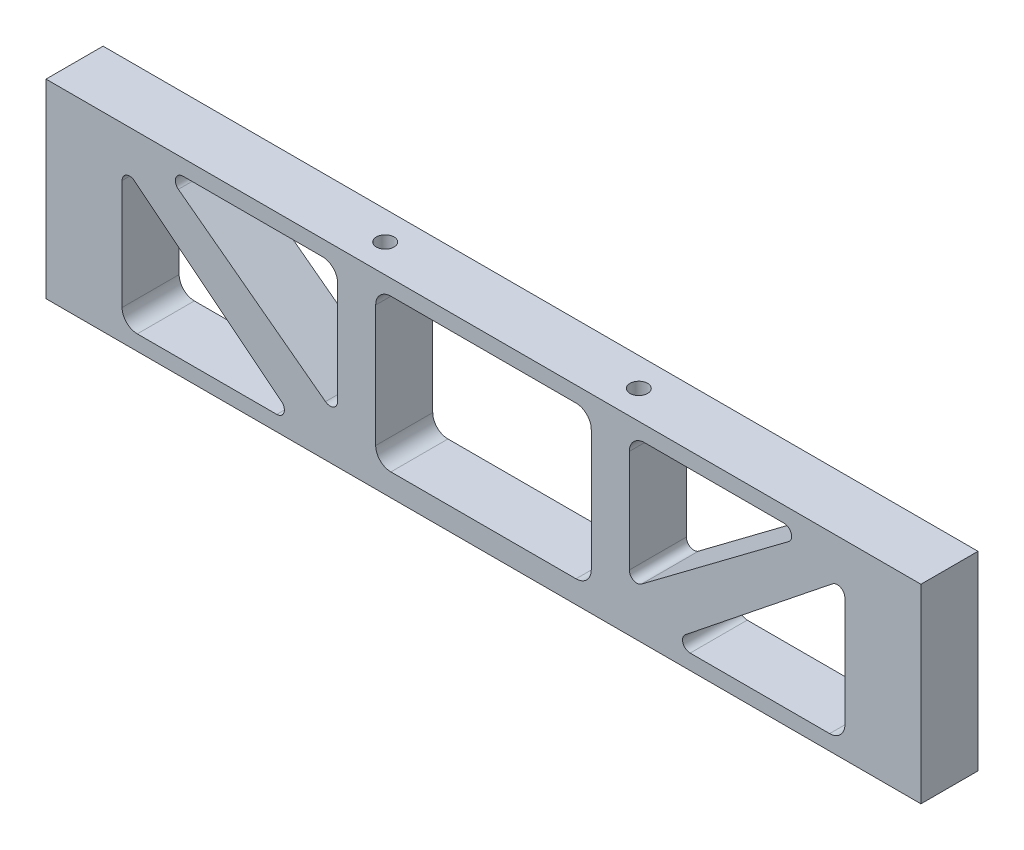
SolidWorks part; units mm, degrees
material "PE High Density"
ref_plane "Front Plane" through (0, 0, 0) normal (0, 0, 1) x (1, 0, 0)
ref_plane "Top Plane" through (0, 0, 0) normal (0, 1, 0) x (1, 0, 0)
ref_plane "Right Plane" through (0, 0, 0) normal (1, 0, 0) x (0, 0, -1)
sketch "Sketch1" plane through (0, 0, 0) normal (0, 0, 1) x (1, 0, 0)
  line L0 (-24.3417, 15.875) -> (-24.3417, -15.875) construction
  line L1 (-73.025, 15.875) -> (73.025, 15.875)
  line L2 (-73.025, 15.875) -> (-73.025, -15.875)
  line L3 (-73.025, -15.875) -> (73.025, -15.875)
  line L4 (73.025, 15.875) -> (73.025, -15.875)
  line L5 (-73.025, 15.875) -> (73.025, -15.875) construction
  line L6 (-73.025, -15.875) -> (73.025, 15.875) construction
  line L7 (24.3417, 15.875) -> (24.3417, -15.875) construction
  line L9 (-69.85, -12.7) -> (-27.5167, 12.7) construction
  line L10 (-69.85, -12.7) -> (-69.85, 12.7) construction
  line L11 (-64.3071, -11.2256) -> (-29.9209, 9.4061)
  line L12 (-73.025, -15.875) -> (-24.3417, -15.875)
  line L13 (-73.025, -15.875) -> (-73.025, 15.875)
  line L14 (-73.025, 15.875) -> (-24.3417, 15.875)
  line L15 (-24.3417, -15.875) -> (-24.3417, 15.875) construction
  line L16 (-69.85, 12.7) -> (-27.5167, 12.7) construction
  line L17 (-27.5167, -12.7) -> (-27.5167, 12.7) construction
  line L18 (-69.85, -12.7) -> (-27.5167, -12.7) construction
  line L19 (-67.4457, -9.4061) -> (-33.0595, 11.2256)
  line L20 (-69.0332, -14.0613) -> (-26.6999, 11.3387) construction
  line L21 (-69.85, -8.0448) -> (-69.85, 11.1125)
  line L22 (-70.6668, -11.3387) -> (-28.3334, 14.0613) construction
  line L23 (-68.2625, 12.7) -> (-33.4679, 12.7)
  line L24 (-63.8988, -12.7) -> (-29.1042, -12.7)
  line L25 (-27.5167, -11.1125) -> (-27.5167, 8.0448)
  line L26 (-15.6238, -11.2256) -> (18.7624, 9.4061)
  line L27 (-18.7624, -9.4061) -> (15.6238, 11.2256)
  line L28 (-21.1667, -8.0448) -> (-21.1667, 11.1125)
  line L29 (-19.5792, 12.7) -> (15.2154, 12.7)
  line L30 (-15.2154, -12.7) -> (19.5792, -12.7)
  line L31 (21.1667, -11.1125) -> (21.1667, 8.0448)
  line L32 (-21.1667, -12.7) -> (21.1667, 12.7) construction
  line L33 (-21.1667, -12.7) -> (-21.1667, 12.7) construction
  line L34 (-21.1667, 12.7) -> (21.1667, 12.7) construction
  line L35 (21.1667, -12.7) -> (21.1667, 12.7) construction
  line L36 (-21.1667, -12.7) -> (21.1667, -12.7) construction
  line L37 (33.0595, -11.2256) -> (67.4457, 9.4061)
  line L38 (29.9209, -9.4061) -> (64.3071, 11.2256)
  line L39 (27.5167, -8.0448) -> (27.5167, 11.1125)
  line L40 (29.1042, 12.7) -> (63.8988, 12.7)
  line L41 (33.4679, -12.7) -> (68.2625, -12.7)
  line L42 (69.85, -11.1125) -> (69.85, 8.0448)
  line L43 (27.5167, -12.7) -> (69.85, 12.7) construction
  line L44 (27.5167, -12.7) -> (27.5167, 12.7) construction
  line L45 (27.5167, 12.7) -> (69.85, 12.7) construction
  line L46 (69.85, -12.7) -> (69.85, 12.7) construction
  line L47 (27.5167, -12.7) -> (69.85, -12.7) construction
  line L59 (-64.3071, -11.2256) -> (-15.6238, -11.2256) construction
  line L60 (-69.85, 15.875) -> (-69.85, -15.875)
  arc A0 (-33.4679, 12.7) -> (-33.0595, 11.2256) centre (-33.4679, 11.9062) cw
  arc A1 (-69.85, -8.0448) -> (-67.4457, -9.4061) centre (-68.2625, -8.0448) ccw
  arc A2 (-69.85, 11.1125) -> (-68.2625, 12.7) centre (-68.2625, 11.1125) cw
  arc A3 (-27.5167, 8.0448) -> (-29.9209, 9.4061) centre (-29.1042, 8.0448) ccw
  arc A4 (-63.8988, -12.7) -> (-64.3071, -11.2256) centre (-63.8988, -11.9062) cw
  arc A5 (-27.5167, -11.1125) -> (-29.1042, -12.7) centre (-29.1042, -11.1125) cw
  arc A6 (15.2154, 12.7) -> (15.6238, 11.2256) centre (15.2154, 11.9062) cw
  arc A7 (-21.1667, -8.0448) -> (-18.7624, -9.4061) centre (-19.5792, -8.0448) ccw
  arc A8 (-21.1667, 11.1125) -> (-19.5792, 12.7) centre (-19.5792, 11.1125) cw
  arc A9 (21.1667, 8.0448) -> (18.7624, 9.4061) centre (19.5792, 8.0448) ccw
  arc A10 (-15.2154, -12.7) -> (-15.6238, -11.2256) centre (-15.2154, -11.9062) cw
  arc A11 (21.1667, -11.1125) -> (19.5792, -12.7) centre (19.5792, -11.1125) cw
  arc A12 (63.8988, 12.7) -> (64.3071, 11.2256) centre (63.8988, 11.9062) cw
  arc A13 (27.5167, -8.0448) -> (29.9209, -9.4061) centre (29.1042, -8.0448) ccw
  arc A14 (27.5167, 11.1125) -> (29.1042, 12.7) centre (29.1042, 11.1125) cw
  arc A15 (69.85, 8.0448) -> (67.4457, 9.4061) centre (68.2625, 8.0448) ccw
  arc A16 (33.4679, -12.7) -> (33.0595, -11.2256) centre (33.4679, -11.9062) cw
  arc A17 (69.85, -11.1125) -> (68.2625, -12.7) centre (68.2625, -11.1125) cw
  point P0 (0, 0)
  point P26 (-30.6022, 12.7)
  point P29 (-69.85, -10.8487)
  point P35 (-27.5167, 10.8487)
  point P38 (-66.7645, -12.7)
  dimension "D7" = 0.7937
  dimension "D8" = 1.5875
  dimension "D9" = 1.5875
  dimension "D10" = 1.5875
  dimension "D11" = 0.7937
  dimension "D12" = 1.5875
  dimension "D1" = 31.75
  dimension "CrossBraceLength" = 146.05
  dimension "D4" = 48.6833
  dimension "D14" = 48.6833
  dimension "D6" = 3.175
  dimension "D2" = 1.5875
  dimension "D5" = 1.5875
  dimension "D3" = 3
  dimension "D13" = 3
extrude "Boss-Extrude1" [suppressed] add sketch "Sketch1" along normal blind 9.525
sketch "Sketch2" plane through (0, 0, 0) normal (0, 0, 1) x (1, 0, 0)
  line L0 (-63.5, 15.3) -> (-63.5, -16.45) construction
  line L1 (-73.025, 15.3) -> (73.025, 15.3)
  line L2 (-73.025, 15.3) -> (-73.025, -16.45)
  line L3 (-73.025, -16.45) -> (73.025, -16.45)
  line L4 (73.025, 15.3) -> (73.025, -16.45)
  line L5 (-73.025, 15.3) -> (73.025, -16.45) construction
  line L6 (-73.025, -16.45) -> (73.025, 15.3) construction
  line L7 (0, 15.3) -> (0, -16.45) construction
  line L8 (-63.5, -16.45) -> (-63.5, 15.3) construction
  line L9 (63.5, 15.3) -> (63.5, -16.45) construction
  line L10 (-21.1667, 15.3) -> (-21.1667, -16.45) construction
  line L11 (-73.025, -0.575) -> (73.025, -0.575) construction
  line L12 (21.1667, 15.3) -> (21.1667, -16.45) construction
  line L14 (-63.5, -16.45) -> (-63.5, 15.3) construction
  line L15 (-63.5, 15.3) -> (-21.1667, 15.3)
  line L19 (-63.5, 15.3) -> (-21.1667, -16.45) construction
  line L20 (-63.5, -16.45) -> (-21.1667, -16.45)
  line L21 (-21.1667, 15.3) -> (-63.5, 15.3)
  line L22 (-63.5, -16.45) -> (-21.1667, -16.45)
  line L23 (-63.5, -16.45) -> (-63.5, 15.3) construction
  line L27 (-63.5, 15.3) -> (-21.1667, -16.45) construction
  line L28 (-50.927, 10.414) -> (-26.3737, -8.001)
  line L29 (-60.325, -11.3725) -> (-60.325, 6.985)
  line L48 (-57.785, -13.9125) -> (-34.5017, -13.9125)
  line L67 (-68.2625, 15.3) -> (-68.2625, -16.45) construction
  line L78 (-58.262, 7.977) -> (-33.7087, -11.6505)
  line L85 (68.2625, 15.875) -> (68.2625, -15.875) construction
  line L96 (73.025, 15.3) -> (73.025, -16.45)
  line L97 (-63.5, 15.3) -> (-24.3417, 15.3)
  line L99 (-60.325, -16.45) -> (-60.325, 15.3) construction
  line L102 (-24.3417, 10.16) -> (-24.3417, -6.985)
  line L104 (-50.165, 12.7) -> (-26.8817, 12.7)
  line L105 (24.3417, 10.16) -> (24.3417, -6.985)
  line L106 (-24.3417, 15.3) -> (-24.3417, -16.45) construction
  line L107 (50.165, 12.7) -> (26.8817, 12.7)
  line L108 (50.927, 10.414) -> (26.3737, -8.001)
  line L109 (57.785, -13.9125) -> (34.5017, -13.9125)
  line L110 (58.262, 7.977) -> (33.7087, -11.6505)
  line L111 (60.325, -11.3725) -> (60.325, 6.985)
  line L112 (0, -16.45) -> (0, -13.275)
  line L114 (-15.4517, 12.7) -> (15.4517, 12.7)
  line L115 (-17.9917, 10.16) -> (-17.9917, -10.16)
  line L116 (-15.4517, -12.7) -> (15.4517, -12.7)
  line L117 (17.9917, 10.16) -> (17.9917, -10.16)
  line L118 (-17.9917, 12.7) -> (17.9917, -12.7) construction
  line L119 (-17.9917, -12.7) -> (17.9917, 12.7) construction
  arc A52 (-57.785, -13.9125) -> (-60.325, -11.3725) centre (-57.785, -11.3725) cw
  arc A53 (-60.325, 6.985) -> (-58.262, 7.977) centre (-59.055, 6.985) cw
  arc A54 (-34.5017, -13.9125) -> (-33.7087, -11.6505) centre (-34.5017, -12.6425) ccw
  arc A55 (-26.8817, 12.7) -> (-24.3417, 10.16) centre (-26.8817, 10.16) cw
  arc A56 (-26.3737, -8.001) -> (-24.3417, -6.985) centre (-25.6117, -6.985) ccw
  arc A57 (-50.927, 10.414) -> (-50.165, 12.7) centre (-50.165, 11.43) cw
  arc A58 (26.3737, -8.001) -> (24.3417, -6.985) centre (25.6117, -6.985) cw
  arc A59 (26.8817, 12.7) -> (24.3417, 10.16) centre (26.8817, 10.16) ccw
  arc A60 (50.927, 10.414) -> (50.165, 12.7) centre (50.165, 11.43) ccw
  arc A61 (57.785, -13.9125) -> (60.325, -11.3725) centre (57.785, -11.3725) ccw
  arc A62 (34.5017, -13.9125) -> (33.7087, -11.6505) centre (34.5017, -12.6425) cw
  arc A63 (60.325, 6.985) -> (58.262, 7.977) centre (59.055, 6.985) ccw
  arc A64 (-15.4517, -12.7) -> (-17.9917, -10.16) centre (-15.4517, -10.16) cw
  arc A65 (-17.9917, 10.16) -> (-15.4517, 12.7) centre (-15.4517, 10.16) cw
  arc A66 (17.9917, 10.16) -> (15.4517, 12.7) centre (15.4517, 10.16) ccw
  arc A67 (17.9917, -10.16) -> (15.4517, -12.7) centre (15.4517, -10.16) cw
  point P18 (-65.405, 13.335)
  point P19 (-23.0717, -18.415)
  point P24 (-63.5, 12.7)
  point P26 (-24.3417, 12.7)
  point P34 (-61.595, 18.415)
  point P36 (-19.2617, -13.335)
  point P65 (0, 0)
  dimension "D6" = 2.54
  dimension "D8" = 1.27
  dimension "D9" = 1.27
  dimension "D11" = 2.54
  dimension "D12" = 1.27
  dimension "D13" = 1.27
  dimension "D16" = 2.54
  dimension "D1" = 146.05
  dimension "D2" = 31.75
  dimension "D3" = 9.525
  dimension "D23" = 4.7625
  dimension "D4" = 42.3333
  dimension "D5" = 42.3333
  dimension "D14" = 3.175
  dimension "D15" = 35.9833
  dimension "D7" = 3.175
  dimension "D10" = 3.175
extrude "Boss-Extrude2" add sketch "Sketch2" along normal blind 9.525
sketch "Sketch3" plane through (-73.025, 0, 0) normal (-1, 0, 0) x (0, 0, 1)
  line L0 (9.525, 15.3) -> (0, 15.3) construction
  line L1 (0, -0.575) -> (9.525, -0.575) construction
  line L3 (4.7625, -16.45) -> (4.7625, 15.3) construction
  line L4 (9.525, -16.45) -> (0, -16.45) construction
  line L5 (0, 15.3) -> (0, -16.45) construction
  line L6 (9.525, 15.3) -> (9.525, -16.45) construction
  circle A0 centre (4.7625, 8) radius 2.2479
  circle A1 centre (4.7625, -9.15) radius 2.2479
  dimension "D2" = 4.4958
  dimension "D1" = 7.3
extrude "Cut-Extrude1" [suppressed] cut sketch "Sketch3" against normal blind 11.1125
sketch "Sketch4" plane through (0, 15.3, 0) normal (0, 1, 0) x (1, 0, 0)
  line L2 (17.9917, -9.525) -> (17.9917, 0) construction
  line L3 (17.9917, -9.525) -> (17.9917, 0) construction
  line L4 (73.025, 0) -> (-73.025, 0)
  line L5 (-73.025, 0) -> (-73.025, -9.525)
  line L6 (-73.025, -9.525) -> (73.025, -9.525)
  line L7 (73.025, -9.525) -> (73.025, 0)
  line L8 (73.025, 0) -> (-73.025, 0) construction
  line L9 (-73.025, 0) -> (-73.025, -9.525) construction
  line L10 (-73.025, -9.525) -> (73.025, -9.525) construction
  line L11 (73.025, -9.525) -> (73.025, 0) construction
  line L12 (-17.9917, -9.525) -> (-17.9917, 0) construction
  line L13 (-17.9917, -9.525) -> (-17.9917, 0) construction
  line L14 (-24.3417, -9.525) -> (-24.3417, 0) construction
  line L15 (-24.3417, -9.525) -> (-24.3417, 0) construction
  line L16 (24.3417, -9.525) -> (24.3417, 0) construction
  line L17 (24.3417, -9.525) -> (24.3417, 0) construction
  line L18 (24.3417, -9.525) -> (17.9917, 0) construction
  line L19 (17.9917, -9.525) -> (24.3417, 0) construction
  circle A0 centre (21.1667, -4.7625) radius 1.4732
  dimension "D2" = 2.9464
  dimension "D1" = 0
extrude "Cut-Extrude2" cut sketch "Sketch4" against normal blind 12.7 contours A0
ref_plane "Plane1" through (0, -0.575, 0) normal (0, 1, 0) x (1, 0, 0)
mirror "Mirror2" about plane through (0, -0.575, 0) normal (0, 1, 0) of "Cut-Extrude2" second plane through (0, 0, 0) second plane normal (1, 0, 0)
mirror "Mirror3" [suppressed] about plane through (0, 0, 0) normal (1, 0, 0)
equation "\"Plate Width\" = 3.5in"
equation "\"Plate Thickness\" = 0.375in"
equation "\"Num holes\" = 4"
equation "\"Plate Height\" = 1.25in"
equation "\"Top Plate Width\" = 4.5in"
equation "\"Plate Clearance Hole Diameter\" = 0.125in"
equation "\"Plate Tap Hole Diameter\" = 0.116in"
equation "\"Bottom Plate Length\" = 6.5in"
equation "\"CrossBraceLength@Sketch1\" = \"Bottom Plate Length\" - 2 * \"Plate Thickness\""
equation "\"D1@Sketch1\"=\"Plate Height\""
equation "\"num_triangle_holes\"= 3"
equation "\"D3@Sketch1\"=\"num_triangle_holes\""
equation "\"D4@Sketch1\"=( \"Bottom Plate Length\" - 2 * \"Plate Thickness\" ) / \"num_triangle_holes\""
equation "\"BorderThickness\"= 0.125"
equation "\"D6@Sketch1\"=\"BorderThickness\""
equation "\"D2@Sketch1\"=\"BorderThickness\"/2"
equation "\"D9@Sketch1\"=\"BorderThickness\"/2"
equation "\"D8@Sketch1\"=\"BorderThickness\"/2"
equation "\"D7@Sketch1\"=\"BorderThickness\"/4"
equation "\"D10@Sketch1\"=\"BorderThickness\"/2"
equation "\"D11@Sketch1\"=\"BorderThickness\"/4"
equation "\"D12@Sketch1\"=\"BorderThickness\"/2"
equation "\"D13@Sketch1\"=\"num_triangle_holes\""
equation "\"D14@Sketch1\"=( \"Bottom Plate Length\" - 2 * \"Plate Thickness\" ) / \"num_triangle_holes\""
equation "\"D1@Boss-Extrude1\"=\"Plate Thickness\""
equation "\"D1@Sketch2\"=\"Bottom Plate Length\" - 2 * \"Plate Thickness\""
equation "\"D2@Sketch2\"=\"Plate Height\""
equation "\"wall_thickness\"= 0.375"
equation "\"D3@Sketch2\"=\"wall_thickness\""
equation "\"D1@Boss-Extrude2\"=\"Plate Thickness\""
equation "\"D23@Sketch2\"=\"wall_thickness\"/2"
equation "\"Number Eight Clearance Size\" = 0.177in"
equation "\"D2@Sketch3\"=\"Number Eight Clearance Size\""
equation "\"D1@Cut-Extrude1\"=(0.75 - \"Plate Thickness\") + 0.0625"
equation "\"D4@Sketch2\"=( ( \"Bottom Plate Length\" - 2 * \"Plate Thickness\" ) - \"Plate Thickness\" * 2 ) /3"
equation "\"D5@Sketch2\"=( ( \"Bottom Plate Length\" - 2 * \"Plate Thickness\" ) - \"Plate Thickness\" * 2 ) /3"
equation "\"D14@Sketch2\"=\"BorderThickness\""
equation "\"D15@Sketch2\"=( ( ( \"Bottom Plate Length\" - 2 * \"Plate Thickness\" ) - \"Plate Thickness\" * 2 ) /3 ) - \"BorderThickness\"*2"
